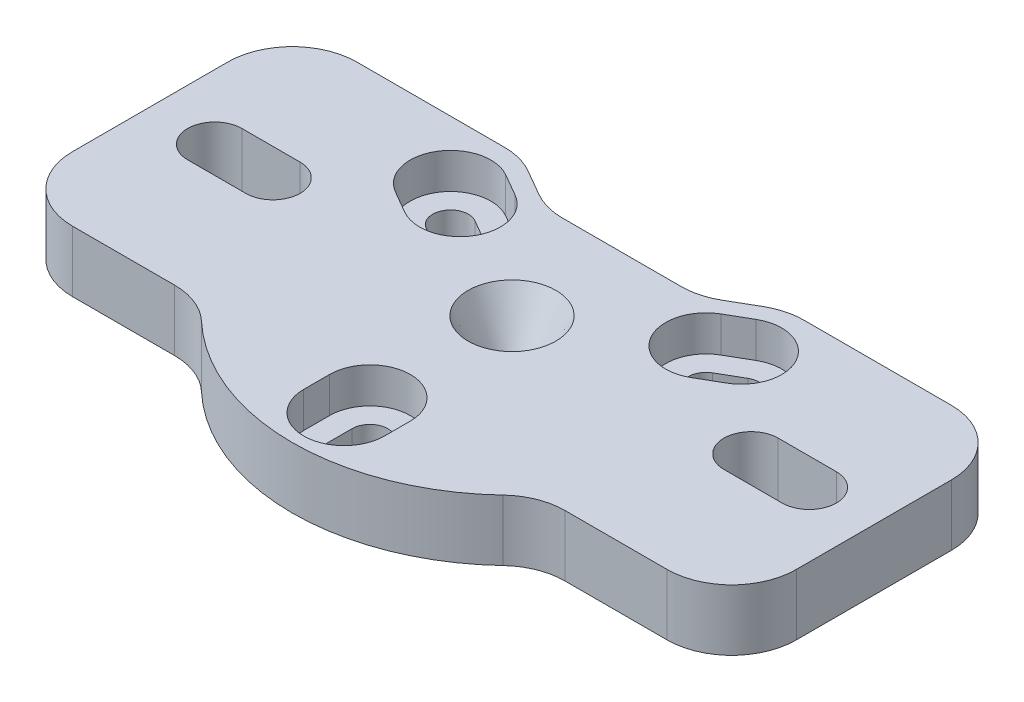
SolidWorks part; units mm, degrees
material "CA"
ref_plane "Front Plane" through (0, 0, 0) normal (0, 0, 1) x (1, 0, 0)
ref_plane "Top Plane" through (0, 0, 0) normal (0, 1, 0) x (1, 0, 0)
ref_plane "Right Plane" through (0, 0, 0) normal (1, 0, 0) x (0, 0, -1)
sketch "Sketch1" plane through (0, 0, 0) normal (0, 1, 0) x (1, 0, 0)
  line L0 (14.7222, 13.97) -> (29.21, 13.97)
  line L1 (-29.21, 13.97) -> (-14.7222, 13.97)
  line L2 (-35.56, 7.62) -> (-35.56, -7.62)
  line L3 (-11.5472, 13.1193) -> (-8.995, 11.6457)
  line L4 (35.56, 7.62) -> (35.56, -7.62)
  line L5 (-23.495, 0) -> (-29.21, 0) construction
  line L6 (-23.495, -2.667) -> (-29.21, -2.667)
  line L7 (-23.495, 2.667) -> (-29.21, 2.667)
  line L8 (23.495, 0) -> (29.21, 0) construction
  line L9 (23.495, 2.667) -> (29.21, 2.667)
  line L10 (23.495, -2.667) -> (29.21, -2.667)
  line L11 (-14.2894, 8.25) -> (0, 0) construction
  line L12 (0, 0) -> (14.2894, 8.25) construction
  line L13 (-15.1644, 6.7345) -> (-12.9647, 5.4645)
  line L14 (-13.4144, 9.7655) -> (-11.2147, 8.4955)
  line L15 (13.4144, 9.7655) -> (11.2147, 8.4955)
  line L16 (15.1644, 6.7345) -> (12.9647, 5.4645)
  line L17 (1.75, -16.5) -> (1.75, -13.96)
  line L18 (-1.75, -13.96) -> (-1.75, -16.5)
  line L19 (-29.21, -13.97) -> (-19.1766, -13.97)
  line L20 (19.1766, -13.97) -> (29.21, -13.97)
  line L21 (-5.82, 10.795) -> (5.82, 10.795)
  line L22 (8.995, 11.6457) -> (11.5472, 13.1193)
  circle A0 centre (0, 0) radius 1.778
  arc A1 (-23.495, -2.667) -> (-23.495, 2.667) centre (-23.495, 0) ccw
  arc A2 (-29.21, 2.667) -> (-29.21, -2.667) centre (-29.21, 0) ccw
  arc A3 (23.495, 2.667) -> (23.495, -2.667) centre (23.495, 0) ccw
  arc A4 (29.21, -2.667) -> (29.21, 2.667) centre (29.21, 0) ccw
  arc A5 (-13.4144, 9.7655) -> (-15.1644, 6.7345) centre (-14.2894, 8.25) ccw
  arc A6 (15.1644, 6.7345) -> (13.4144, 9.7655) centre (14.2894, 8.25) ccw
  circle A7 centre (0, 0) radius 20 construction
  arc A8 (29.21, 13.97) -> (35.56, 7.62) centre (29.21, 7.62) cw
  arc A9 (29.21, -13.97) -> (35.56, -7.62) centre (29.21, -7.62) ccw
  arc A10 (19.1766, -13.97) -> (14.8183, -15.7018) centre (19.1766, -20.32) ccw
  arc A11 (-29.21, 13.97) -> (-35.56, 7.62) centre (-29.21, 7.62) ccw
  circle A12 centre (0, 0) radius 16.5 construction
  arc A13 (-1.75, -16.5) -> (1.75, -16.5) centre (0, -16.5) ccw
  arc A14 (5.82, 10.795) -> (8.995, 11.6457) centre (5.82, 17.145) ccw
  arc A15 (11.5472, 13.1193) -> (14.7222, 13.97) centre (14.7222, 7.62) cw
  arc A16 (-14.7222, 13.97) -> (-11.5472, 13.1193) centre (-14.7222, 7.62) cw
  arc A17 (-12.9647, 5.4645) -> (-11.2147, 8.4955) centre (-12.0897, 6.98) ccw
  arc A18 (11.2147, 8.4955) -> (12.9647, 5.4645) centre (12.0897, 6.98) ccw
  arc A19 (1.75, -13.96) -> (-1.75, -13.96) centre (0, -13.96) ccw
  arc A20 (-14.8183, -15.7018) -> (14.8183, -15.7018) centre (0, 0) ccw
  arc A21 (-19.1766, -13.97) -> (-14.8183, -15.7018) centre (-19.1766, -20.32) cw
  arc A22 (-29.21, -13.97) -> (-35.56, -7.62) centre (-29.21, -7.62) cw
  arc A23 (-8.995, 11.6457) -> (-5.82, 10.795) centre (-5.82, 17.145) ccw
  point P9 (-26.3525, 0)
  point P14 (26.3525, 0)
  point P42 (11.6397, 13.97)
  point P50 (-16.4611, -13.97)
  dimension "D3" = 3.556
  dimension "D10" = 40
  dimension "D11" = 6.35
  dimension "D8" = 33
  dimension "D9" = 3.5
  dimension "D13" = 10.795
  dimension "D18" = 6.35
  dimension "D16" = 21.59
  dimension "D21" = 6.35
  dimension "D14" = 6.35
  dimension "D2" = 71.12
  dimension "D4" = 23.495
  dimension "D5" = 23.495
  dimension "D6" = 29.21
  dimension "D7" = 5.334
  dimension "D12" = 120
  dimension "D15" = 13.97
  dimension "D17" = 35.56
  dimension "D19" = 2.54
  dimension "D20" = 13.97
  dimension "D22" = 5.588
  dimension "D23" = 5.588
extrude "Boss-Extrude1" add sketch "Sketch1" along normal blind 6
sketch "Sketch5" plane through (0, 6, 0) normal (0, 1, 0) x (1, 0, 0)
  line L0 (-3.9688, -13.96) -> (-3.9688, -16.5)
  line L1 (3.9688, -16.5) -> (3.9688, -13.96)
  line L2 (12.305, 11.687) -> (10.1053, 10.417)
  line L3 (16.2738, 4.813) -> (14.0741, 3.543)
  line L4 (-12.305, 11.687) -> (-10.1053, 10.417)
  line L5 (-16.2738, 4.813) -> (-14.0741, 3.543)
  arc A0 (16.2738, 4.813) -> (12.305, 11.687) centre (14.2894, 8.25) ccw
  arc A1 (-12.305, 11.687) -> (-16.2738, 4.813) centre (-14.2894, 8.25) ccw
  arc A2 (-3.9688, -16.5) -> (3.9688, -16.5) centre (0, -16.5) ccw
  arc A3 (-14.0741, 3.543) -> (-10.1053, 10.417) centre (-12.0897, 6.98) ccw
  arc A4 (3.9688, -13.96) -> (-3.9688, -13.96) centre (0, -13.96) ccw
  arc A5 (10.1053, 10.417) -> (14.0741, 3.543) centre (12.0897, 6.98) ccw
  dimension "D1" = 7.9375
extrude "Cut-Extrude1" cut sketch "Sketch5" against normal blind 3.5
ref_plane "Plane1" through (0, 0, 0) normal (0.5, 0, 0.866) x (0.866, 0, -0.5)
chamfer "Chamfer1" distance 2.54 distance2 5.08 1 edges at (0, 6, 1.778)
